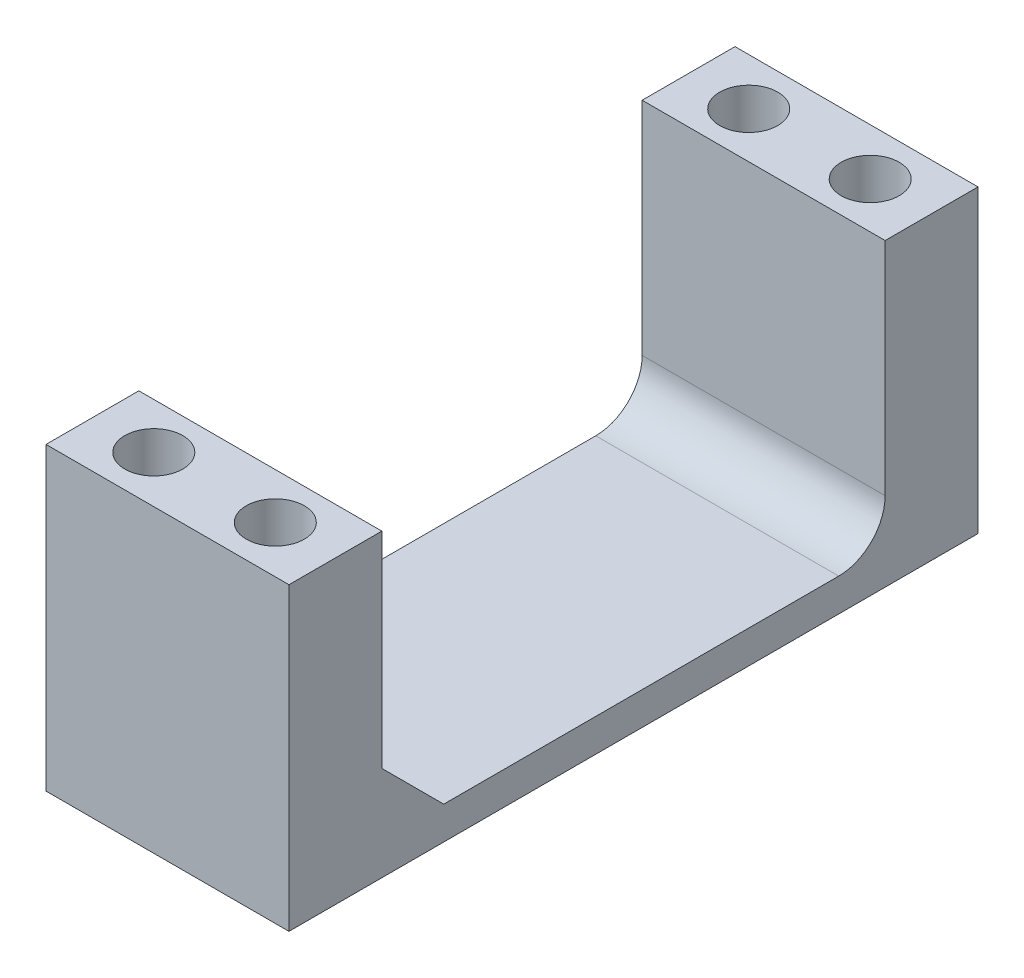
SolidWorks part; units mm, degrees
material "ABS"
ref_plane "Front Plane" through (0, 0, 0) normal (0, 0, 1) x (1, 0, 0)
ref_plane "Top Plane" through (0, 0, 0) normal (0, 1, 0) x (1, 0, 0)
ref_plane "Right Plane" through (0, 0, 0) normal (1, 0, 0) x (0, 0, -1)
sketch "Sketch3" plane through (0, 0, 0) normal (1, 0, 0) x (0, 0, -1)
  line L0 (30.7871, 3.5919) -> (30.7871, -18.3521)
  line L1 (30.2791, 3.5919) -> (37.3911, 3.5919) construction
  line L2 (30.7871, -18.3521) -> (-10.5133, -18.3521)
  line L3 (-10.5133, -18.3521) -> (-10.5133, 3.5919)
  line L4 (-10.0053, 3.5919) -> (-17.1173, 3.5919) construction
  line L5 (-10.5133, 3.5919) -> (-18.1333, 3.5919)
  line L6 (-18.1333, 3.5919) -> (-18.1333, -21.0461)
  line L7 (-18.1333, -21.0461) -> (38.4071, -21.0461)
  line L8 (38.4071, -21.0461) -> (38.4071, 3.5919)
  line L9 (38.4071, 3.5919) -> (30.7871, 3.5919)
  line L12 (30.2791, -4.6603) -> (30.2791, 3.5919) construction
  line L16 (-10.0053, -4.6603) -> (-10.0053, 3.5919) construction
  dimension "D1" = 2.694
  dimension "D2" = 24.638
  dimension "D3" = 0.508
  dimension "D4" = 0.508
  dimension "D5" = 7.62
extrude "Boss-Extrude3" add sketch "Sketch3" against normal up to vertex from vertex
chamfer "Chamfer2" distance 5.08 angle 45 1 edges at (54.4297, -18.3521, 10.5133)
fillet "Fillet2" radius 3.81 1 edges at (54.4297, -18.3521, -30.7871)
sketch "Sketch4" plane through (0, 0, 0) normal (0, 1, 0) x (1, 0, 0)
  circle A0 centre (49.445, 34.5463) radius 2.3812
  circle A1 centre (59.4145, 34.5463) radius 2.3812
  circle A2 centre (49.445, -14.2725) radius 2.3813
  circle A3 centre (59.4145, -14.2725) radius 2.3813
  dimension "D1" = 4.7625
extrude "Cut-Extrude1" cut sketch "Sketch4" against normal through all both and the other way through all contours A0
